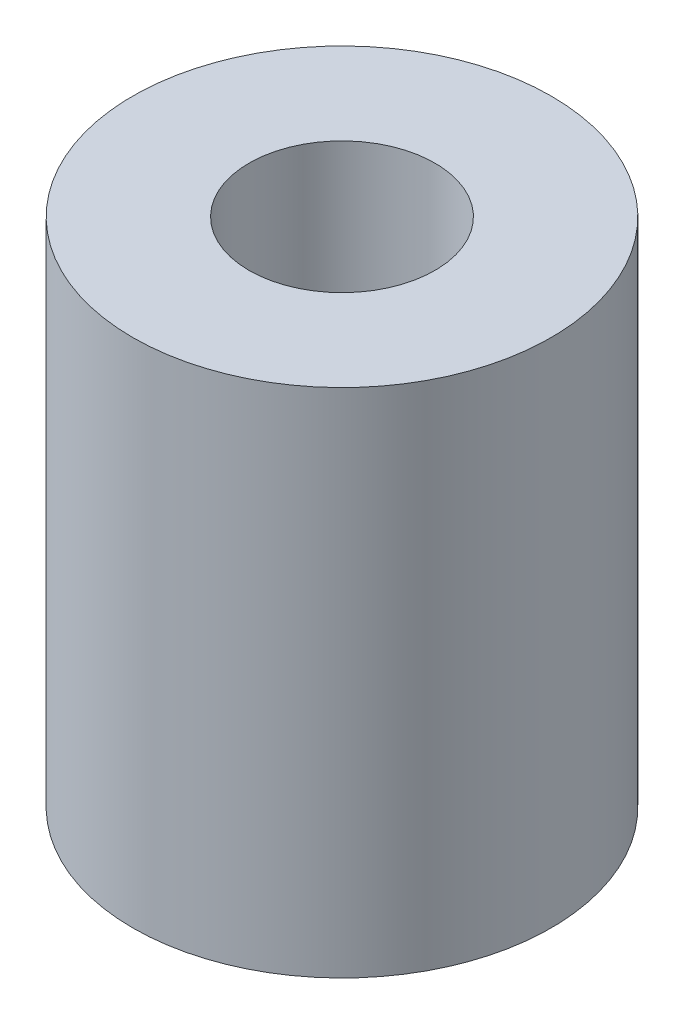
SolidWorks part; units mm, degrees
ref_plane "Front Plane" through (0, 0, 0) normal (0, 0, 1) x (1, 0, 0)
ref_plane "Top Plane" through (0, 0, 0) normal (0, 1, 0) x (1, 0, 0)
ref_plane "Right Plane" through (0, 0, 0) normal (1, 0, 0) x (0, 0, -1)
sketch "Sketch1" plane through (0, 0, 0) normal (0, 1, 0) x (1, 0, 0)
  circle A0 centre (0, 0) radius 36
  circle A1 centre (0, 0) radius 16
  dimension "D1" = 72
  dimension "D2" = 32
extrude "Boss-Extrude1" add sketch "Sketch1" along normal blind 88
